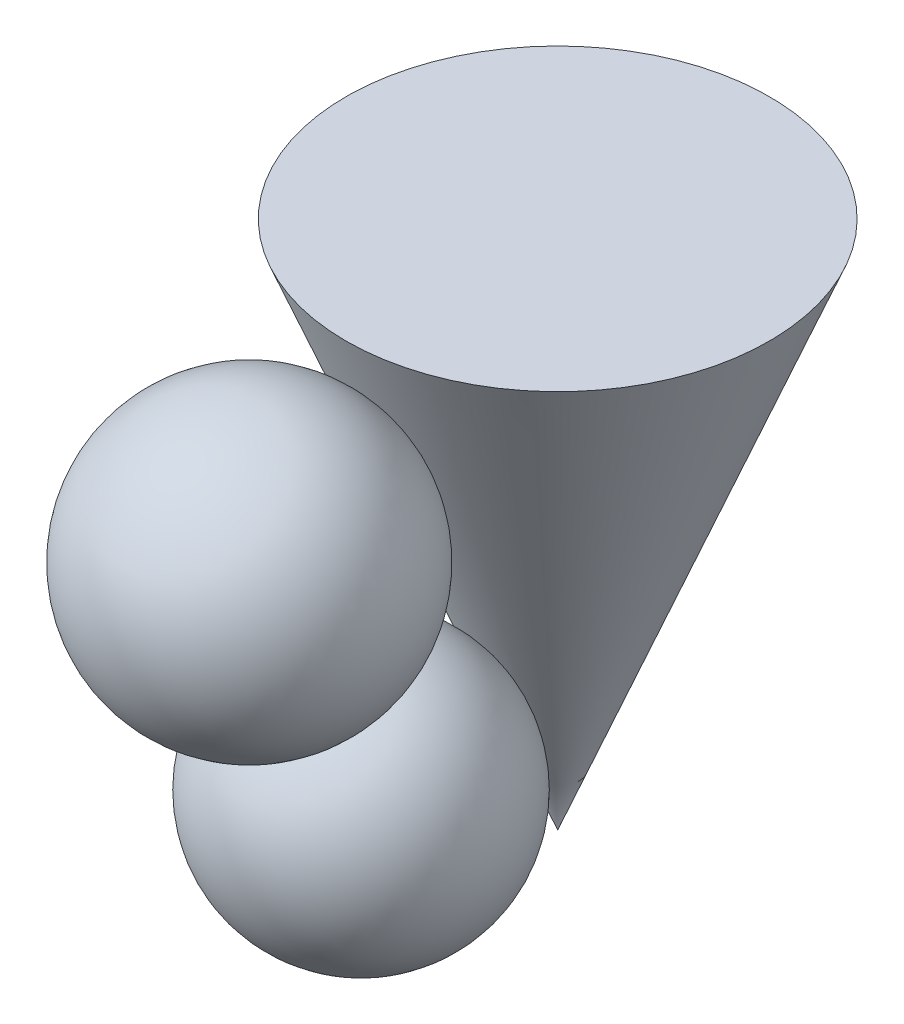
SolidWorks part; units mm, degrees
ref_plane "Front" through (0, 0, 0) normal (0, 0, 1) x (1, 0, 0)
ref_plane "Top" through (0, 0, 0) normal (0, 1, 0) x (1, 0, 0)
ref_plane "Right" through (0, 0, 0) normal (1, 0, 0) x (0, 0, -1)
sketch "Sketch1" plane through (0, 0, 0) normal (0, 1, 0) x (1, 0, 0)
  point P0 (0, 0)
ref_plane "Plane1" through (0, 100, 0) normal (0, 1, 0) x (-1, 0, 0)
sketch "Sketch2" plane through (0, 100, 0) normal (0, 1, 0) x (-1, 0, 0)
  circle A0 centre (0, 0) radius 40
loft "Cone" add profiles "Sketch2", "Sketch1"
sketch "Sketch3" plane through (0, 0, 0) normal (0, 0, 1) x (1, 0, 0)
  line L0 (40, 100) -> (-40, 100) construction
  line L1 (-40, 100) -> (0, 0) construction
  line L2 (0, 0) -> (40, 100) construction
  line L3 (0, 72.9187) -> (58.2783, 72.9187) construction
  line L4 (58.3349, 72.9187) -> (0, 0) construction
  line L6 (0, 0) -> (64.0844, 0) construction
  circle A0 centre (0, 72.9187) radius 27.0813 construction
  circle A1 centre (58.3349, 72.9187) radius 27.0813 construction
  circle A2 centre (37.1623, 25.1601) radius 25.1601 construction
ref_plane "Plane2" through (0, 72.9187, 0) normal (0, 1, 0) x (-1, 0, 0)
sketch "Sketch4" plane through (0, 72.9187, 0) normal (0, 1, 0) x (-1, 0, 0)
  line L0 (0, 0) -> (0, 58.2783) construction
  circle A0 centre (0, 0) radius 58.2783 construction
ref_plane "Plane3" through (0, 0, 58.2783) normal (0, 0, 1) x (1, 0, 0)
sketch "Sketch5" plane through (0, 0, 58.2783) normal (0, 0, 1) x (1, 0, 0)
  line L0 (0, 100) -> (0, 45.8374)
  arc A0 (0, 45.8374) -> (0, 100) centre (0, 72.9187) ccw
revolve "SphereB" add sketch "Sketch5" angle 360 about L0
ref_plane "Plane4" through (0, 25.1601, 0) normal (0, 1, 0) x (-1, 0, 0)
sketch "Sketch6" plane through (0, 25.1601, 0) normal (0, 1, 0) x (-1, 0, 0)
  line L0 (0, 0) -> (0, 37.1623) construction
  circle A0 centre (0, 0) radius 37.1623
ref_plane "Plane5" through (0, 0, 37.1623) normal (0, 0, 1) x (1, 0, 0)
sketch "Sketch7" plane through (0, 0, 37.1623) normal (0, 0, 1) x (1, 0, 0)
  line L0 (0, 50.3202) -> (0, 0)
  arc A0 (0, 0) -> (0, 50.3202) centre (0, 25.1601) ccw
revolve "SphereA" add sketch "Sketch7" angle 360 about L0
ref_plane "Plane6" through (0, 0, -66.4295) normal (0, 0, 1) x (1, 0, 0)
sketch "Vertical Trace" plane through (0, 0, -66.4295) normal (0, 0, 1) x (1, 0, 0)
  line L1 (-132.7391, 0) -> (-84.2058, 137.1126)
  line L2 (-132.7391, 0) -> (0, 0) construction
  dimension "D1" = 70.508
sketch "Horizontal Trace" plane through (0, 0, 0) normal (0, 1, 0) x (1, 0, 0)
  line L0 (-132.7391, 66.4295) -> (-23.5027, -60.1198)
ref_plane "Touching Plane" through (-40.3111, 14.2688, 34.7963) normal (-0.7312, 0.2588, 0.6312) x (0.595, -0.2106, 0.7757)
